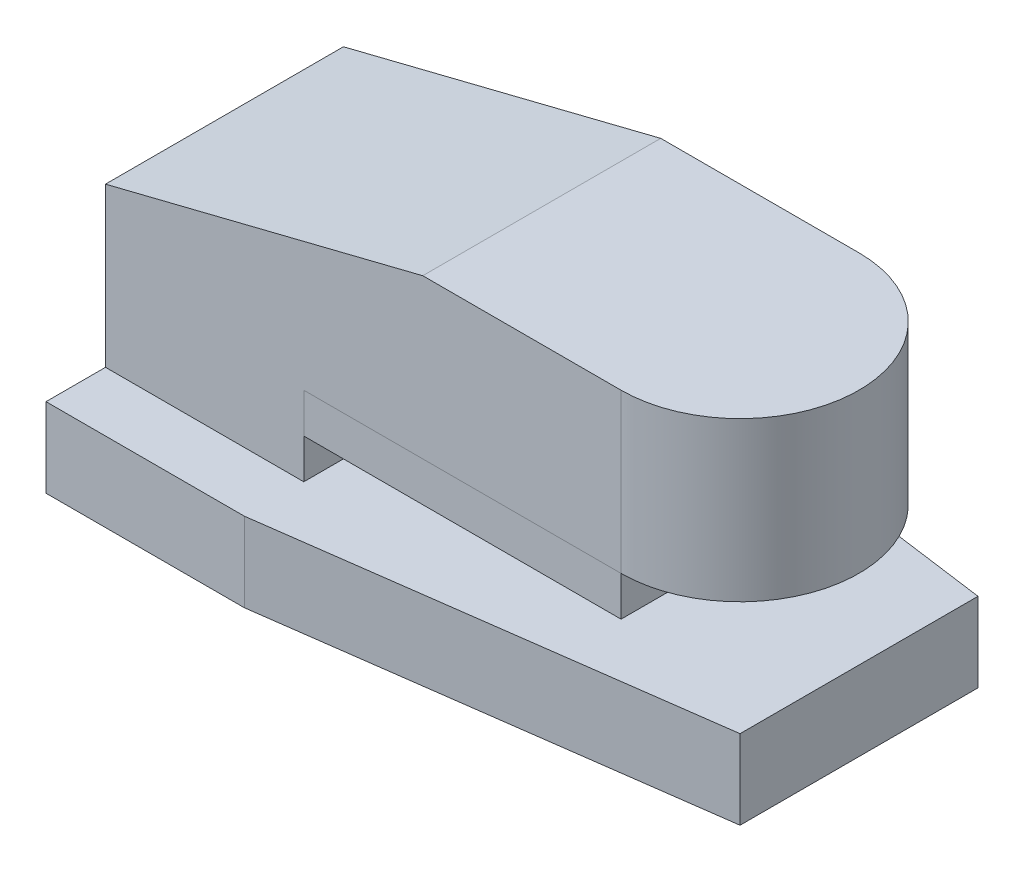
SolidWorks part; units mm, degrees
ref_plane "Front Plane" through (0, 0, 0) normal (0, 0, 1) x (1, 0, 0)
ref_plane "Top Plane" through (0, 0, 0) normal (0, 1, 0) x (1, 0, 0)
ref_plane "Right Plane" through (0, 0, 0) normal (1, 0, 0) x (0, 0, -1)
sketch "Sketch1" plane through (0, 0, 0) normal (0, 1, 0) x (1, 0, 0)
  line L0 (50, 0) -> (160, 15)
  line L1 (0, 0) -> (50, 0)
  line L2 (0, 0) -> (0, 90)
  line L3 (0, 90) -> (50, 90)
  line L4 (160, 15) -> (160, 75)
  line L5 (160, 75) -> (50, 90)
  dimension "D1" = 160
  dimension "D2" = 90
  dimension "D3" = 15
  dimension "D4" = 15
  dimension "D5" = 110
  dimension "D6" = 110
extrude "Extrude1" add sketch "Sketch1" along normal blind 20
ref_plane "Plane1" through (0, 0, -15) normal (0, 0, 1) x (1, 0, 0)
sketch "Sketch2" plane through (0, 0, -15) normal (0, 0, 1) x (1, 0, 0)
  line L0 (0, 20) -> (0, 60)
  line L1 (80, 80) -> (160, 80)
  line L2 (160, 80) -> (160, 40)
  line L3 (160, 40) -> (50, 40)
  line L4 (50, 40) -> (50, 20)
  line L5 (0, 20) -> (50, 20) construction
  line L6 (50, 20) -> (0, 20)
  line L7 (0, 60) -> (80, 80)
  line L8 (160, 20) -> (160, 0) construction
  line L9 (50, 20) -> (50, 0) construction
  dimension "D1" = 20
  dimension "D2" = 20
  dimension "D3" = 40
  dimension "D4" = 80
extrude "Extrude2" add sketch "Sketch2" against normal blind 60 separate body
sketch "Sketch3" plane through (0, 80, 0) normal (0, 1, 0) x (1, 0, 0)
  line L0 (160, 45) -> (130, 45) construction
  line L1 (160, 75) -> (160, 15) construction
  line L2 (160, 75) -> (80, 75) construction
  line L3 (130, 75) -> (160, 75)
  line L4 (160, 75) -> (160, 15)
  line L5 (-44, 15) -> (44, 15) construction
  line L6 (160, 15) -> (130, 15)
  arc A0 (130, 15) -> (130, 75) centre (130, 45) ccw
  line M1 (80, 15) -> (160, 15)
  line M2 (160, 15) -> (160, 75)
  line M3 (160, 75) -> (80, 75)
sketch "Sketch4" plane through (0, 0, -15) normal (0, 0, 1) x (1, 0, 0)
  line L1 (50, 40) -> (130, 40)
  line L2 (50, 40) -> (50, 30)
  line L3 (50, 30) -> (130, 30)
  line L4 (130, 40) -> (130, 30)
  line L5 (130, 30) -> (129.446, 30.3147)
  line L6 (160, 40) -> (160, 80) construction
  dimension "D1" = 30
  dimension "D2" = 10
extrude "Extrude8" cut sketch "Sketch3" against normal blind 40 contours A0 M1 M2 | A0 L4 M3
extrude "Extrude9" add sketch "Sketch4" against normal blind 60 separate body
